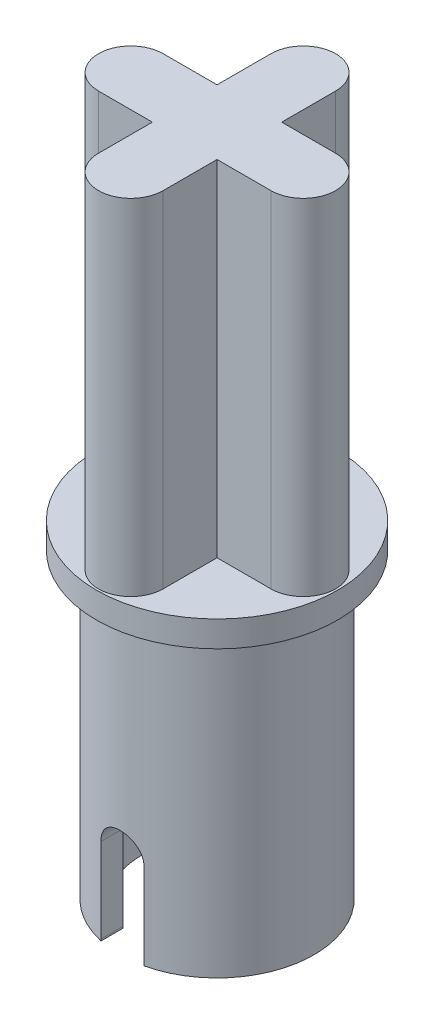
SolidWorks part; units mm, degrees
ref_plane "Front Plane" through (0, 0, 0) normal (0, 0, 1) x (1, 0, 0)
ref_plane "Top Plane" through (0, 0, 0) normal (0, 1, 0) x (1, 0, 0)
ref_plane "Right Plane" through (0, 0, 0) normal (1, 0, 0) x (0, 0, -1)
sketch "Sketch1" plane through (0, 0, 0) normal (0, 1, 0) x (1, 0, 0)
  circle A0 centre (0, 0) radius 2.8
  dimension "D1" = 5.6
extrude "Boss-Extrude1" add sketch "Sketch1" along normal blind 0.6
sketch "Sketch2" plane through (0, 0.6, 0) normal (0, 1, 0) x (1, 0, 0)
  line L0 (0, -2.8) -> (0, -2) construction
  line L1 (0, 2.8) -> (0, 2) construction
  line L2 (-2.8, 0) -> (-2, 0) construction
  line L3 (2.8, 0) -> (2, 0) construction
  line L4 (0, -2) -> (0, 2) construction
  line L5 (-0.75, -2) -> (-0.75, 2)
  line L6 (0.75, -2) -> (0.75, 2)
  line L7 (-2, 0) -> (2, 0) construction
  line L8 (-2, 0.75) -> (2, 0.75)
  line L9 (-2, -0.75) -> (2, -0.75)
  circle A0 centre (0, 0) radius 2.8 construction
  arc A1 (-0.75, -2) -> (0.75, -2) centre (0, -2) ccw
  arc A2 (0.75, 2) -> (-0.75, 2) centre (0, 2) ccw
  arc A3 (-2, 0.75) -> (-2, -0.75) centre (-2, 0) ccw
  arc A4 (2, -0.75) -> (2, 0.75) centre (2, 0) ccw
  point P12 (0, 0)
  point P17 (0, 0)
  point P22 (0, 0)
  point P23 (0, 0)
  point P24 (0, 0)
  point P25 (0, 0)
  point P26 (0, 0)
  dimension "D1" = 0.8
  dimension "D2" = 0.8
  dimension "D3" = 0.8
extrude "Boss-Extrude2" add sketch "Sketch2" along normal blind 8 contours L9 A4 L8 L6 | L6 A2 L5 L8 | L5 L9 L6 L8 | L8 A3 L9 L5 | L5 A1 L6 L9
sketch "Sketch6" plane through (0, 0, 0) normal (0, -1, 0) x (1, 0, 0)
  circle A0 centre (0, 0) radius 2.25
  dimension "D1" = 4.5
extrude "Boss-Extrude3" add sketch "Sketch6" along normal blind 7
ref_plane "Plane1" through (0, 0, 100) normal (0, 0, 1) x (1, 0, 0)
sketch "Sketch7" plane through (0, 0, 100) normal (0, 0, 1) x (1, 0, 0)
  line L0 (0, 0) -> (0, -5) construction
  line L1 (0, -5) -> (0, -6.9622) construction
  line L2 (0.5, -5) -> (0.5, -6.9622)
  line L3 (-0.5, -5) -> (-0.5, -6.9622)
  arc A0 (0.5, -5) -> (-0.5, -5) centre (0, -5) ccw
  arc A1 (-0.5, -6.9622) -> (0.5, -6.9622) centre (0, -6.9622) ccw
  point P3 (0, -5.9811)
extrude "Cut-Extrude1" cut sketch "Sketch7" against normal through all
ref_plane "Plane6" through (0, -10, 0) normal (0, 1, 0) x (1, 0, 0)
sketch "Sketch9" plane through (0, -10, 0) normal (0, 1, 0) x (1, 0, 0)
  circle A0 centre (0, 0) radius 1.75
  dimension "D1" = 3.5
extrude "Cut-Extrude3" cut sketch "Sketch9" along normal blind 10
